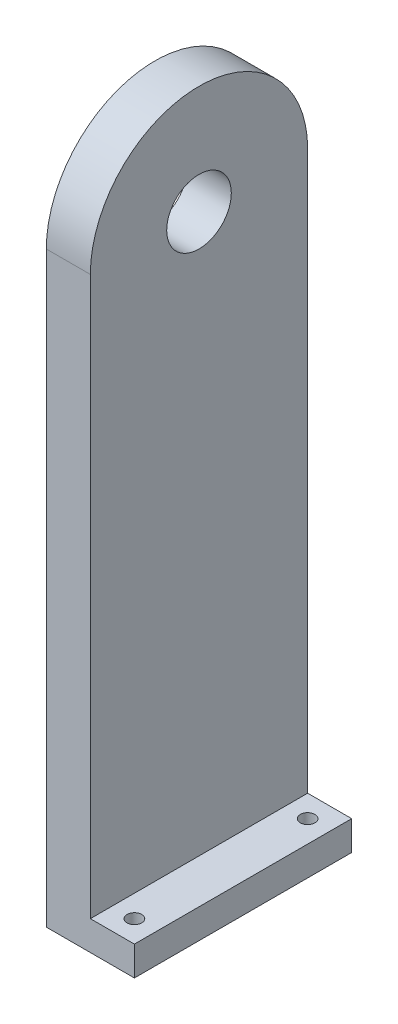
SolidWorks part; units mm, degrees
material "ABS"
ref_plane "Front Plane" through (0, 0, 0) normal (0, 0, 1) x (1, 0, 0)
ref_plane "Top Plane" through (0, 0, 0) normal (0, 1, 0) x (1, 0, 0)
ref_plane "Right Plane" through (0, 0, 0) normal (1, 0, 0) x (0, 0, -1)
sketch "Sketch1" plane through (0, 0, 0) normal (1, 0, 0) x (0, 0, -1)
  line L0 (-37, 0) -> (-37, -200)
  line L1 (-37, -200) -> (37, -200)
  line L2 (37, -200) -> (37, 0)
  circle A0 centre (0, 0) radius 22 construction
  arc A1 (37, 0) -> (-37, 0) centre (0, 0) ccw
  dimension "D1" = 44
  dimension "D2" = 15
  dimension "D3" = 200
extrude "Boss-Extrude1" add sketch "Sketch1" along normal blind 15
sketch "Sketch2" plane through (0, -200, 0) normal (0, -1, 0) x (1, 0, 0)
  line L0 (15, -37) -> (0, -37) construction
  line L1 (15, 37) -> (30, 37)
  line L2 (15, 37) -> (15, -37)
  line L3 (15, -37) -> (30, -37)
  line L4 (30, 37) -> (30, -37)
  dimension "D1" = 15
extrude "Boss-Extrude2" add sketch "Sketch2" against normal blind 10
sketch "Sketch3" plane through (0, -200, 0) normal (0, -1, 0) x (1, 0, 0)
  line L0 (30, -37) -> (30, 37) construction
  line L1 (30, 37) -> (0, 37) construction
  line L2 (30, -37) -> (0, -37) construction
  circle A0 centre (22.5, 29.5) radius 2.5
  circle A1 centre (22.5, -29.5) radius 2.5
  dimension "D1" = 5
  dimension "D2" = 5
  dimension "D3" = 7.5
  dimension "D4" = 7.5
  dimension "D5" = 7.5
  dimension "D6" = 7.5
extrude "Cut-Extrude1" cut sketch "Sketch3" against normal blind 10
sketch "Sketch4" plane through (0, 0, 0) normal (-1, 0, 0) x (0, 0, 1)
  circle A0 centre (0, 0) radius 11
  dimension "D1" = 22
extrude "Cut-Extrude2" cut sketch "Sketch4" against normal through all
